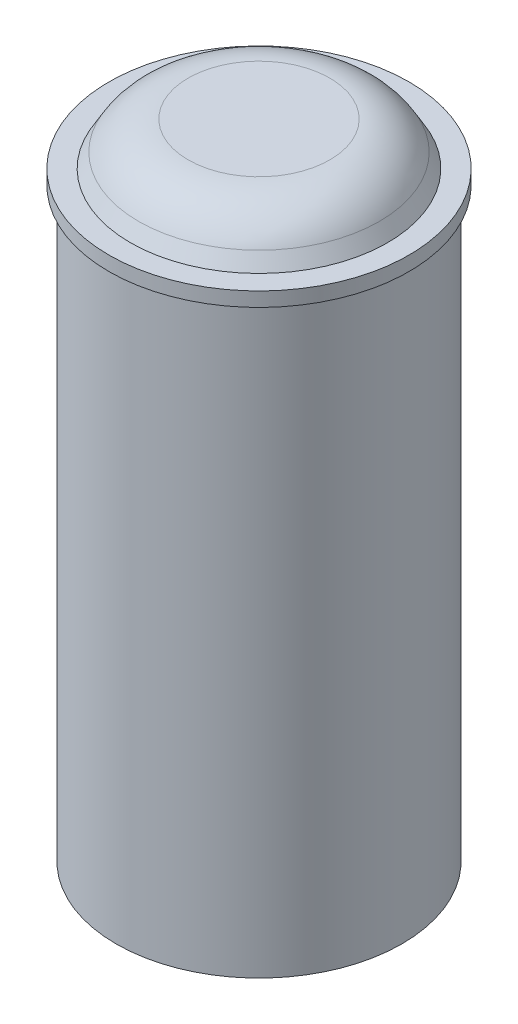
SolidWorks part; units mm, degrees
ref_plane "Front Plane" through (0, 0, 0) normal (0, 0, 1) x (1, 0, 0)
ref_plane "Top Plane" through (0, 0, 0) normal (0, 1, 0) x (1, 0, 0)
ref_plane "Right Plane" through (0, 0, 0) normal (1, 0, 0) x (0, 0, -1)
sketch "Sketch1" plane through (0, 0, 0) normal (0, 1, 0) x (1, 0, 0)
  circle A0 centre (0, 0) radius 12.7
  dimension "D1" = 25.4
extrude "Boss-Extrude1" add sketch "Sketch1" along normal blind 1.27
sketch "Sketch2" plane through (0, 1.27, 0) normal (0, 1, 0) x (1, 0, 0)
  line L0 (0, 0) -> (0, 12.7) construction
  line L1 (0, 0) -> (8.9803, 8.9803) construction
  line L2 (0, 0) -> (12.7, 0) construction
  line L3 (0, 0) -> (8.9803, -8.9803) construction
  line L4 (0, 0) -> (0, -12.7) construction
  line L5 (0, 0) -> (-8.9803, -8.9803) construction
  line L6 (0, 0) -> (-12.7, 0) construction
  line L7 (0, 0) -> (-8.9803, 8.9803) construction
  circle A0 centre (0, 0) radius 12.7
  circle A1 centre (0, 0) radius 11.43
  circle A2 centre (0, 0) radius 2.54
  circle A3 centre (0, 6.35) radius 1.27
  circle A4 centre (4.4901, 4.4901) radius 1.27
  circle A5 centre (6.35, 0) radius 1.27
  circle A6 centre (4.4901, -4.4901) radius 1.27
  circle A7 centre (0, -6.35) radius 1.27
  circle A8 centre (-4.4901, -4.4901) radius 1.27
  circle A9 centre (-6.35, 0) radius 1.27
  circle A10 centre (-4.4901, 4.4901) radius 1.27
  point P31 (0, 0)
  circle M1 centre (0, 0) radius 12.7
  dimension "D1" = 25.4
  dimension "D2" = 1.27
  dimension "D3" = 5.08
  dimension "D4" = 2.54
  dimension "D5" = 8
extrude "Boss-Extrude2" add sketch "Sketch2" along normal blind 50.8 contours A1 M1 | A9 | A10 | A8 | A2 | A3 | A4 | A5 | A6 | A7
sketch "Sketch3" plane through (0, 52.07, 0) normal (0, 1, 0) x (1, 0, 0)
  circle A0 centre (0, 0) radius 13.335
  dimension "D1" = 26.67
extrude "Boss-Extrude3" add sketch "Sketch3" along normal blind 1.27
sketch "Sketch4" plane through (0, 53.34, 0) normal (0, 1, 0) x (1, 0, 0)
  circle A0 centre (0, 0) radius 11.43
  dimension "D1" = 22.86
extrude "Boss-Extrude4" add sketch "Sketch4" along normal blind 3.81 draft 30
fillet "Fillet1" radius 5.08 1 edges at (0, 57.15, 9.2303)
